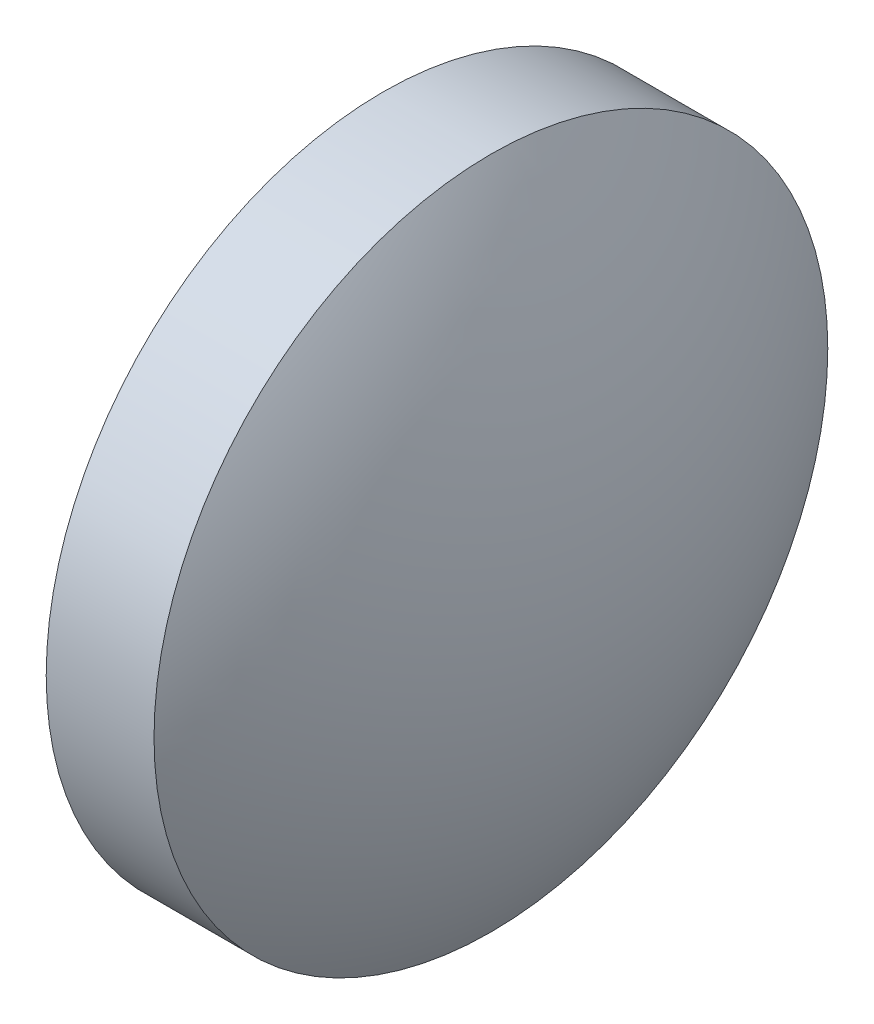
SolidWorks part; units mm, degrees
ref_plane "前视基准面" through (0, 0, 0) normal (0, 0, 1) x (1, 0, 0)
ref_plane "上视基准面" through (0, 0, 0) normal (0, 1, 0) x (1, 0, 0)
ref_plane "右视基准面" through (0, 0, 0) normal (1, 0, 0) x (0, 0, -1)
sketch "草图1" plane through (0, 0, 0) normal (0, 0, 1) x (1, 0, 0)
  line L0 (41.5483, 30.1753) -> (43.5483, 30.1753)
  line L1 (43.5483, 30.1753) -> (43.5483, 17.6753)
  line L2 (43.5483, 17.6753) -> (41.5483, 17.6753)
  line L3 (41.5483, 17.6753) -> (41.5483, 30.1753)
  line L4 (36.0197, 23.9253) -> (46.5325, 23.9253) construction
  arc A0 (41.5483, 30.1753) -> (41.5483, 17.6753) centre (51.6646, 23.9253) ccw
  arc A1 (43.5483, 17.6753) -> (43.5483, 30.1753) centre (33.4323, 23.9253) ccw
  dimension "D1" = 2
  dimension "D2" = 12.5
revolve "旋转1" add sketch "草图1" angle 360 about L4
